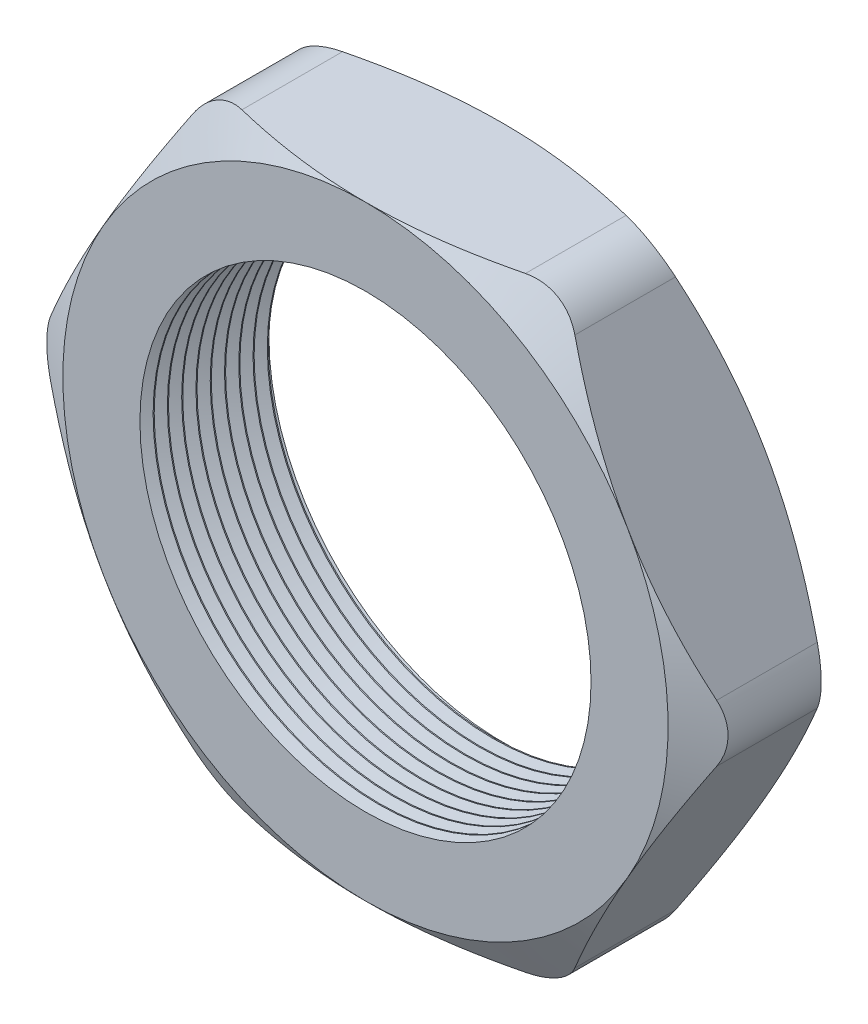
SolidWorks part; units mm, degrees
ref_plane "Front Plane" through (0, 0, 0) normal (0, 0, 1) x (1, 0, 0)
ref_plane "Top Plane" through (0, 0, 0) normal (0, 1, 0) x (1, 0, 0)
ref_plane "Right Plane" through (0, 0, 0) normal (1, 0, 0) x (0, 0, -1)
sketch "Sketch1" plane through (0, 0, 0) normal (0, 0, 1) x (1, 0, 0)
  line L1 (-15.5446, 0) -> (-7.7723, -13.462)
  line L2 (-7.7723, -13.462) -> (7.7723, -13.462)
  line L3 (7.7723, -13.462) -> (15.5446, 0)
  line L4 (15.5446, 0) -> (7.7723, 13.462)
  line L5 (7.7723, 13.462) -> (-7.7723, 13.462)
  line L6 (-7.7723, 13.462) -> (-15.5446, 0)
  circle A0 centre (0, 0) radius 13.462 construction
  circle A1 centre (0, 0) radius 10.033
  dimension "TS" = 20.066
  dimension "H" = 26.924
extrude "Extrude1" add sketch "Sketch1" along normal blind 6.096
sketch "Sketch2" plane through (0, 0, 6.096) normal (0, 0, 1) x (1, 0, 0)
  line L0 (7.7723, 13.462) -> (-7.7723, 13.462) construction
  circle A0 centre (0, 0) radius 13.462
extrude "Cut-Extrude1" cut sketch "Sketch2" against normal through all draft 60 flip side to cut
sketch "Sketch3" plane through (0, 0, 0) normal (0, 0, -1) x (-1, 0, 0)
  line L0 (-7.7723, 13.462) -> (7.7723, 13.462) construction
  circle A0 centre (0, 0) radius 13.462
extrude "Cut-Extrude2" cut sketch "Sketch3" against normal through all draft 60 flip side to cut
fillet "Fillet1" radius 2.54 6 edges at (15.5446, 0, 3.048) (7.7723, -13.462, 3.048) (-7.7723, -13.462, 3.048) (-15.5446, 0, 3.048) (-7.7723, 13.462, 3.048) (7.7723, 13.462, 3.048)
sketch "Sketch4" plane through (0, 0, 0) normal (0, 1, 0) x (1, 0, 0)
  line L0 (-10.033, -6.096) -> (-10.033, -5.5094)
  line L1 (-10.033, 0) -> (-10.033, -6.096) construction
  line L2 (-10.033, -5.5094) -> (-10.541, -5.8027)
  line L3 (-10.541, -5.8027) -> (-10.033, -6.096)
  dimension "D1" = 60
  dimension "D2" = 60
  dimension "D3" = 0.508
revolve "Cut-Revolve1" cut sketch "Sketch4" angle 360 about axis through (0, 0, 0) along (0, 0, 1)
pattern_linear "LPattern1" count 10 spacing 0.635 along (0, 0, -1) of "Cut-Revolve1"
